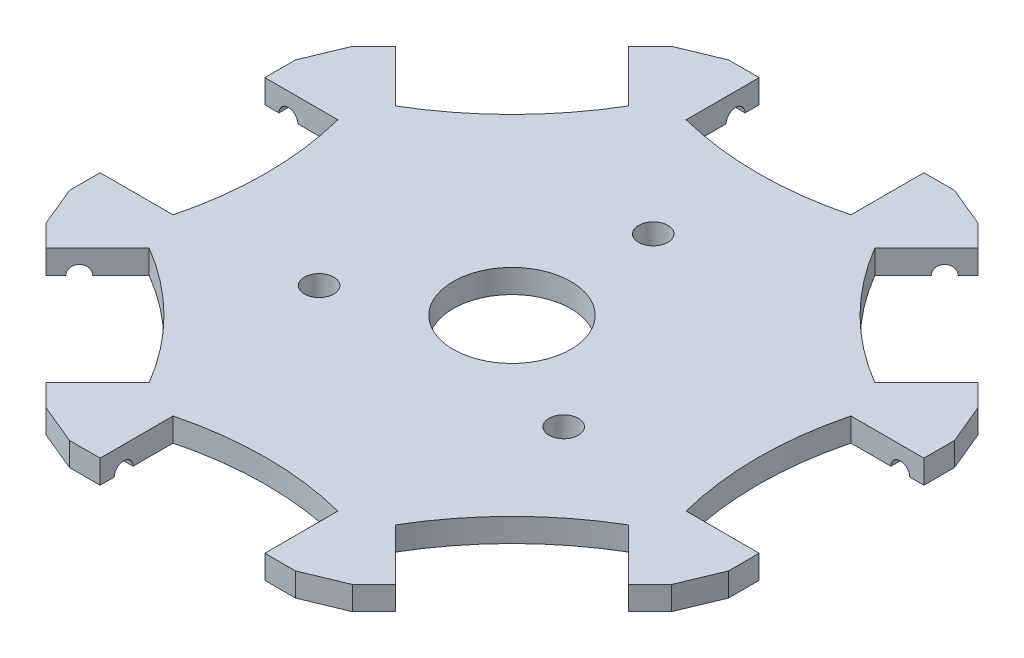
SolidWorks part; units mm, degrees
ref_plane "Front Plane" through (0, 0, 0) normal (0, 0, 1) x (1, 0, 0)
ref_plane "Top Plane" through (0, 0, 0) normal (0, 1, 0) x (1, 0, 0)
ref_plane "Right Plane" through (0, 0, 0) normal (1, 0, 0) x (0, 0, -1)
sketch "Sketch2" plane through (0, 0, 0) normal (0, 1, 0) x (1, 0, 0)
  line L0 (-7, 28) -> (7, 28)
  line L1 (28, -11.598) -> (28, 11.598)
  line L2 (28, 11.598) -> (11.598, 28)
  line L3 (11.598, 28) -> (-11.598, 28)
  line L4 (-11.598, 28) -> (-28, 11.598)
  line L5 (-28, 11.598) -> (-28, -11.598)
  line L6 (-28, -11.598) -> (-11.598, -28)
  line L7 (-11.598, -28) -> (11.598, -28)
  line L8 (11.598, -28) -> (28, -11.598)
  line L9 (-7, 28) -> (-7, 21.8)
  line L10 (7, 28) -> (7, 21.8)
  line L11 (24.7488, 14.8493) -> (20.3647, 10.4652)
  line L12 (14.8493, 24.7488) -> (10.4652, 20.3647)
  line L13 (28, -7) -> (21.8, -7)
  line L14 (28, 7) -> (21.8, 7)
  line L15 (14.8493, -24.7488) -> (10.4652, -20.3647)
  line L16 (24.7488, -14.8493) -> (20.3647, -10.4652)
  line L17 (-7, -28) -> (-7, -21.8)
  line L18 (7, -28) -> (7, -21.8)
  line L19 (-24.7488, -14.8493) -> (-20.3647, -10.4652)
  line L20 (-14.8493, -24.7488) -> (-10.4652, -20.3647)
  line L21 (-28, 7) -> (-21.8, 7)
  line L22 (-28, -7) -> (-21.8, -7)
  line L23 (-14.8493, 24.7488) -> (-10.4652, 20.3647)
  line L24 (-24.7488, 14.8493) -> (-20.3647, 10.4652)
  circle A0 centre (0, 0) radius 28 construction
  circle A1 centre (0, 0) radius 5
  arc A2 (7, 21.8) -> (-7, 21.8) centre (0, 48.9109) cw
  arc A3 (20.3647, 10.4652) -> (10.4652, 20.3647) centre (34.5853, 34.5853) cw
  arc A4 (21.8, -7) -> (21.8, 7) centre (48.9109, 0) cw
  arc A5 (10.4652, -20.3647) -> (20.3647, -10.4652) centre (34.5853, -34.5853) cw
  arc A6 (-7, -21.8) -> (7, -21.8) centre (0, -48.9109) cw
  arc A7 (-20.3647, -10.4652) -> (-10.4652, -20.3647) centre (-34.5853, -34.5853) cw
  arc A8 (-21.8, 7) -> (-21.8, -7) centre (-48.9109, 0) cw
  arc A9 (-10.4652, 20.3647) -> (-20.3647, 10.4652) centre (-34.5853, 34.5853) cw
  point P54 (0, 0)
  dimension "D5" = 28
  dimension "D7" = 10
  dimension "D1" = 23.196
  dimension "D2" = 14
  dimension "D3" = 6.2
  dimension "D4" = 4.598
  dimension "D6" = 8
extrude "Boss-Extrude2" add sketch "Sketch2" along normal blind 2 contours A2 L9 L3 L4 L5 L6 L7 L8 L1 L2 L10 A1
sketch "Sketch3" plane through (7, 0, 0) normal (-1, 0, 0) x (0, 0, 1)
  line L0 (-28, 0) -> (-21.8, 0) construction
  circle A0 centre (-26, 0) radius 0.8
  dimension "D1" = 1.6
  dimension "D2" = 2
extrude "Cut-Extrude1" cut sketch "Sketch3" against normal blind 2
sketch "Sketch4" plane through (-7, 0, 0) normal (1, 0, 0) x (0, 0, -1)
  line L0 (28, 0) -> (21.8, 0) construction
  circle A0 centre (26, 0) radius 0.8
  dimension "D1" = 1.6
  dimension "D2" = 2
extrude "Cut-Extrude2" cut sketch "Sketch4" against normal blind 2
chamfer "Chamfer1" distance 2 distance2 2 8 edges at (11.598, 1, -28) (-11.598, 1, -28) (-28, 1, -11.598) (-28, 1, 11.598) (-11.598, 1, 28) (11.598, 1, 28) (28, 1, 11.598) (28, 1, -11.598)
pattern_circular "CirPattern3" count 8 every 45 about axis through (0, 0, 0) along (0, 1, 0) of "Cut-Extrude1", "Cut-Extrude2"
hole_wizard "Ø2.5mm Dowel Hole1" positions "Sketch6" profile "Sketch5" hole size "Ø2.5" standard "ANSI Metric"
sketch "Sketch6" plane through (0, 2, 0) normal (0, 1, 0) x (1, 0, 0)
  point P0 (0, 12)
  point P9 (10.3923, -6)
  point P10 (-10.3923, -6)
  point P12 (0, 0)
  dimension "D1" = 12
  dimension "D2" = 3
sketch "Sketch5" plane through (0, 2, -12) normal (1, 0, 0) x (0, 0, 1)
  line L0 (0, 0) -> (0, 10.7511)
  line L1 (0, 10.7511) -> (1.25, 10)
  line L2 (1.25, 10) -> (1.25, 0)
  line L5 (1.25, 0) -> (0, 0)
  line L10 (0, 10.7511) -> (-1.25, 10) construction
  line L11 (0, -6.35) -> (0, 107.95) construction
  dimension "Hole Dia." = 2.5
  dimension "Hole Depth" = 10
  dimension "Drill Angle" = 118
